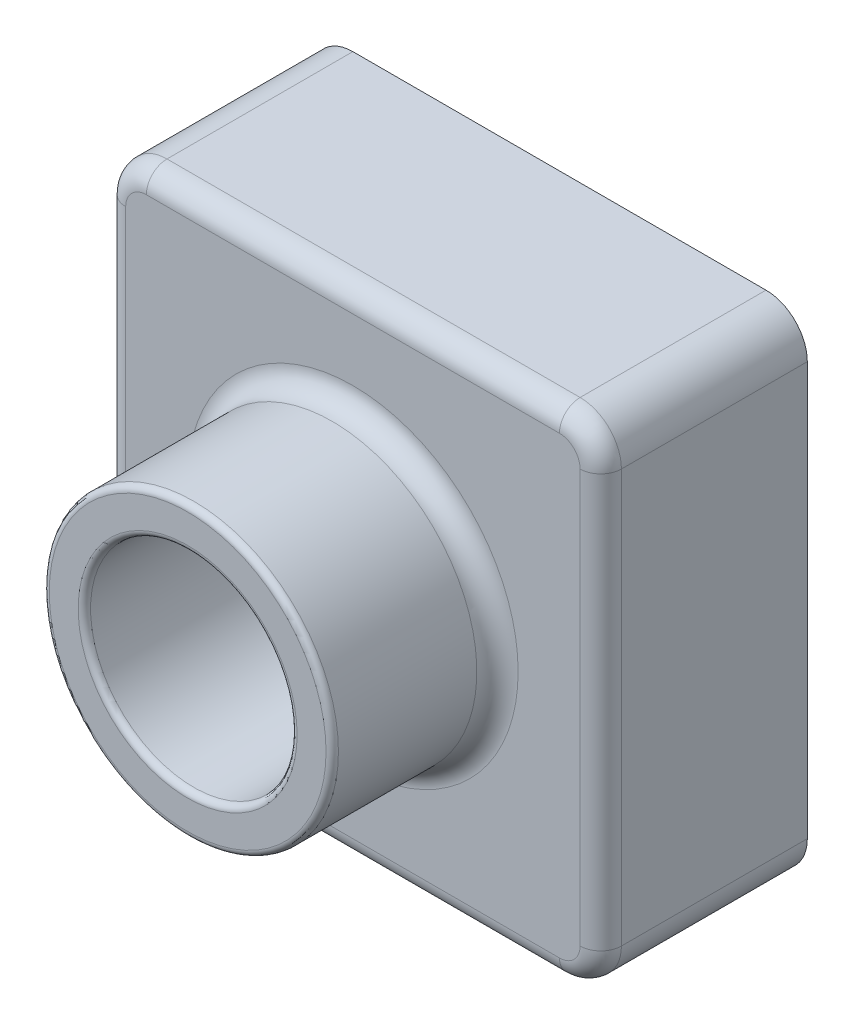
SolidWorks part; units mm, degrees
material "Chrome Stainless Steel"
ref_plane "Front Plane" through (0, 0, 0) normal (0, 0, 1) x (1, 0, 0)
ref_plane "Top Plane" through (0, 0, 0) normal (0, 1, 0) x (1, 0, 0)
ref_plane "Right Plane" through (0, 0, 0) normal (1, 0, 0) x (0, 0, -1)
other "Configuration Table"
sketch "Sketch2" plane through (0, 0, 0) normal (0, 0, 1) x (1, 0, 0)
  line L1 (0, 0) -> (120, 0)
  line L2 (0, 0) -> (0, 120)
  line L3 (0, 120) -> (120, 120)
  line L4 (120, 0) -> (120, 120)
  dimension "D1" = 120
  dimension "D2" = 120
extrude "Boss-Extrude1" add sketch "Sketch2" along normal blind 50
sketch "Sketch4" plane through (0, 0, 50) normal (0, 0, 1) x (1, 0, 0)
  line L0 (120, 120) -> (0, 120) construction
  line L1 (0, 120) -> (0, 0) construction
  circle A0 centre (60, 60) radius 35
  dimension "D1" = 60
  dimension "D3" = 70
  dimension "D2" = 60
extrude "Boss-Extrude2" add sketch "Sketch4" along normal blind 40
sketch "Sketch6" plane through (0, 0, 90) normal (0, 0, 1) x (1, 0, 0)
  circle A0 centre (60, 60) radius 25
  dimension "D1" = 50
extrude "Cut-Extrude1" cut sketch "Sketch6" against normal through all
fillet "Fillet1" radius 10 4 edges at (0, 0, 25) (120, 0, 25) (120, 120, 25) (0, 120, 25)
fillet "Fillet2" radius 1.5 2 edges at (95, 60, 90) (85, 60, 90)
fillet "Fillet3" radius 5 9 edges at (25, 60, 50) (2.9289, 117.0711, 50) (60, 120, 50) (117.0711, 117.0711, 50) (120, 60, 50) (117.0711, 2.9289, 50) (60, 0, 50) (2.9289, 2.9289, 50) (0, 60, 50)
shell "Shell1" thickness 2
